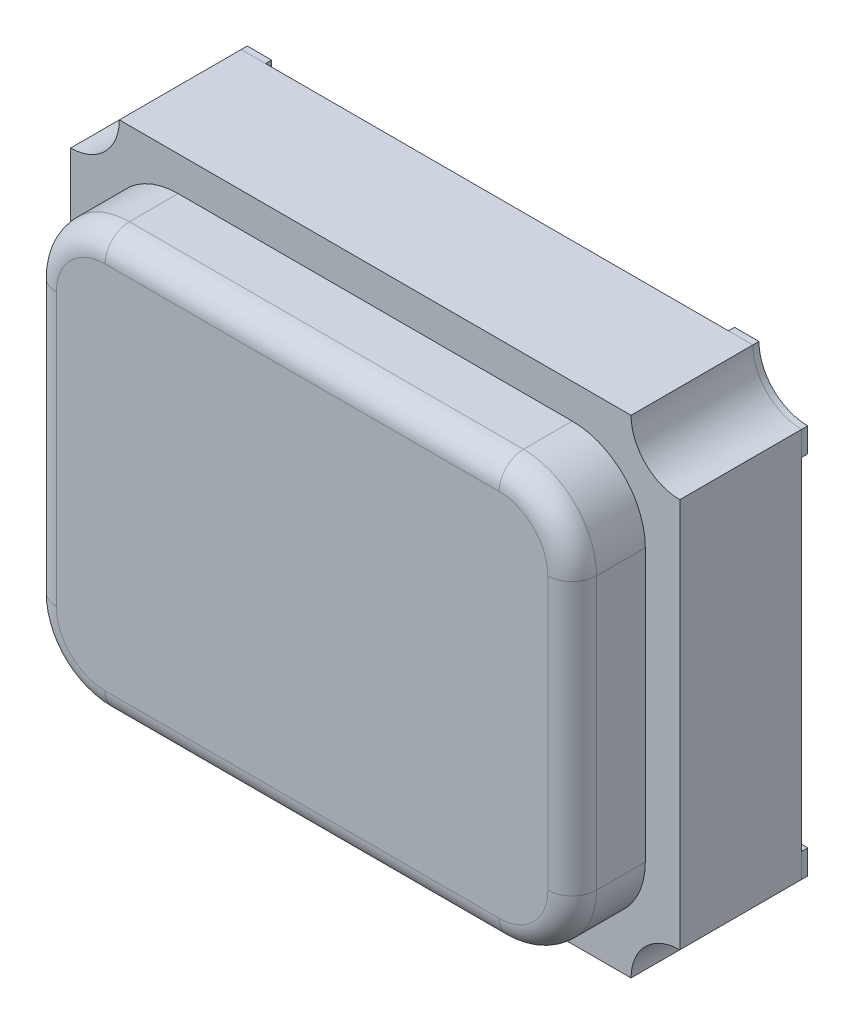
SolidWorks part; units mm, degrees
ref_plane "Front Plane" through (0, 0, 0) normal (0, 0, 1) x (1, 0, 0)
ref_plane "Top Plane" through (0, 0, 0) normal (0, 1, 0) x (1, 0, 0)
ref_plane "Right Plane" through (0, 0, 0) normal (1, 0, 0) x (0, 0, -1)
sketch "Sketch1" plane through (0, 0, 0) normal (0, 0, 1) x (1, 0, 0)
  line L1 (-1.25, 1) -> (1.25, 1)
  line L2 (-1.25, 1) -> (-1.25, -1)
  line L3 (-1.25, -1) -> (1.25, -1)
  line L5 (1.25, 1) -> (1.25, -1)
extrude "Boss-Extrude1" add sketch "Sketch1" along normal blind 0.5
sketch "Sketch2" plane through (0, 0, 0.5) normal (0, 0, 1) x (1, 0, 0)
  circle A0 centre (-1.25, 1) radius 0.2
  circle A1 centre (1.25, 1) radius 0.2
  circle A2 centre (-1.25, -1) radius 0.2
  circle A3 centre (1.25, -1) radius 0.2
extrude "Cut-Extrude1" cut sketch "Sketch2" against normal blind 0.5
sketch "Sketch3" plane through (0, 0, 0.5) normal (0, 0, 1) x (1, 0, 0)
  line L0 (-1.1086, 0.5586) -> (-1.1086, -0.5586)
  line L1 (-0.8086, -0.8586) -> (0.8086, -0.8586)
  line L2 (1.1086, -0.5586) -> (1.1086, 0.5586)
  line L3 (0.8086, 0.8586) -> (-0.8086, 0.8586)
  arc A0 (-1.25, 0.8) -> (-1.05, 1) centre (-1.25, 1) ccw construction
  arc A1 (-1.05, -1) -> (-1.25, -0.8) centre (-1.25, -1) ccw construction
  arc A2 (1.25, -0.8) -> (1.05, -1) centre (1.25, -1) ccw construction
  arc A3 (1.05, 1) -> (1.25, 0.8) centre (1.25, 1) ccw construction
  arc A4 (-1.1086, -0.5586) -> (-0.8086, -0.8586) centre (-0.8086, -0.5586) ccw
  arc A5 (0.8086, -0.8586) -> (1.1086, -0.5586) centre (0.8086, -0.5586) ccw
  arc A6 (1.1086, 0.5586) -> (0.8086, 0.8586) centre (0.8086, 0.5586) ccw
  arc A7 (-1.1086, 0.5586) -> (-0.8086, 0.8586) centre (-0.8086, 0.5586) cw
  point P18 (-1.1086, -0.8586)
  point P21 (1.1086, -0.8586)
  point P24 (1.1086, 0.8586)
  point P27 (-1.1086, 0.8586)
  dimension "D1" = 0.3
extrude "Boss-Extrude2" add sketch "Sketch3" along normal blind 0.3
sketch "Sketch4" plane through (0, 0, 0) normal (0, 0, -1) x (-1, 0, 0)
  line L0 (0.45, -0.3) -> (0.3, -0.45)
  line L1 (-1.05, 1) -> (1.05, 1) construction
  line L2 (-0.95, 0.9) -> (-0.3, 0.9)
  line L3 (0.95, -0.9) -> (0.3, -0.9)
  line L4 (1.15, -0.3) -> (0.45, -0.3)
  line L5 (-1.15, 0.3) -> (-0.3, 0.3)
  line L6 (0.3, -0.45) -> (0.3, -0.9)
  line L7 (-0.3, 0.9) -> (-0.3, 0.3)
  line L9 (-1.25, 0.7) -> (-1.15, 0.7)
  line L10 (-1.25, 0.8) -> (-1.25, 0.7)
  line L11 (-1.25, -0.8) -> (-1.25, 0.8) construction
  line L12 (-1.15, 0.7) -> (-1.15, 0.3)
  line L13 (-1.05, 1) -> (-0.95, 1)
  line L14 (-0.95, 1) -> (-0.95, 0.9)
  line L15 (0.95, 1) -> (0.95, 0.9)
  line L16 (1.05, 1) -> (0.95, 1)
  line L17 (1.15, 0.7) -> (1.15, 0.3)
  line L18 (1.25, 0.8) -> (1.25, 0.7)
  line L19 (1.25, 0.7) -> (1.15, 0.7)
  line L20 (0.3, 0.9) -> (0.3, 0.3)
  line L21 (1.15, 0.3) -> (0.3, 0.3)
  line L22 (0.95, 0.9) -> (0.3, 0.9)
  line L25 (1.25, -0.7) -> (1.15, -0.7)
  line L26 (1.25, -0.8) -> (1.25, -0.7)
  line L27 (1.15, -0.7) -> (1.15, -0.3)
  line L28 (1.05, -1) -> (0.95, -1)
  line L29 (0.95, -1) -> (0.95, -0.9)
  line L30 (-0.95, -1) -> (-0.95, -0.9)
  line L31 (-1.05, -1) -> (-0.95, -1)
  line L32 (-1.15, -0.7) -> (-1.15, -0.3)
  line L33 (-1.25, -0.8) -> (-1.25, -0.7)
  line L34 (-1.25, -0.7) -> (-1.15, -0.7)
  line L35 (-0.3, -0.9) -> (-0.3, -0.3)
  line L36 (-1.15, -0.3) -> (-0.3, -0.3)
  line L37 (-0.95, -0.9) -> (-0.3, -0.9)
  arc A0 (-1.25, 0.8) -> (-1.05, 1) centre (-1.25, 1) ccw
  arc A1 (1.25, 0.8) -> (1.05, 1) centre (1.25, 1) cw
  arc A2 (1.25, -0.8) -> (1.05, -1) centre (1.25, -1) ccw
  arc A3 (-1.25, -0.8) -> (-1.05, -1) centre (-1.25, -1) cw
extrude "Boss-Extrude3" add sketch "Sketch4" along normal blind 0.025 separate body
fillet "Fillet1" radius 0.1 8 edges at (-1.1086, 0, 0.8) (-1.0207, 0.7707, 0.8) (0, 0.8586, 0.8) (1.0207, 0.7707, 0.8) (1.1086, 0, 0.8) (1.0207, -0.7707, 0.8) (0, -0.8586, 0.8) (-1.0207, -0.7707, 0.8)
